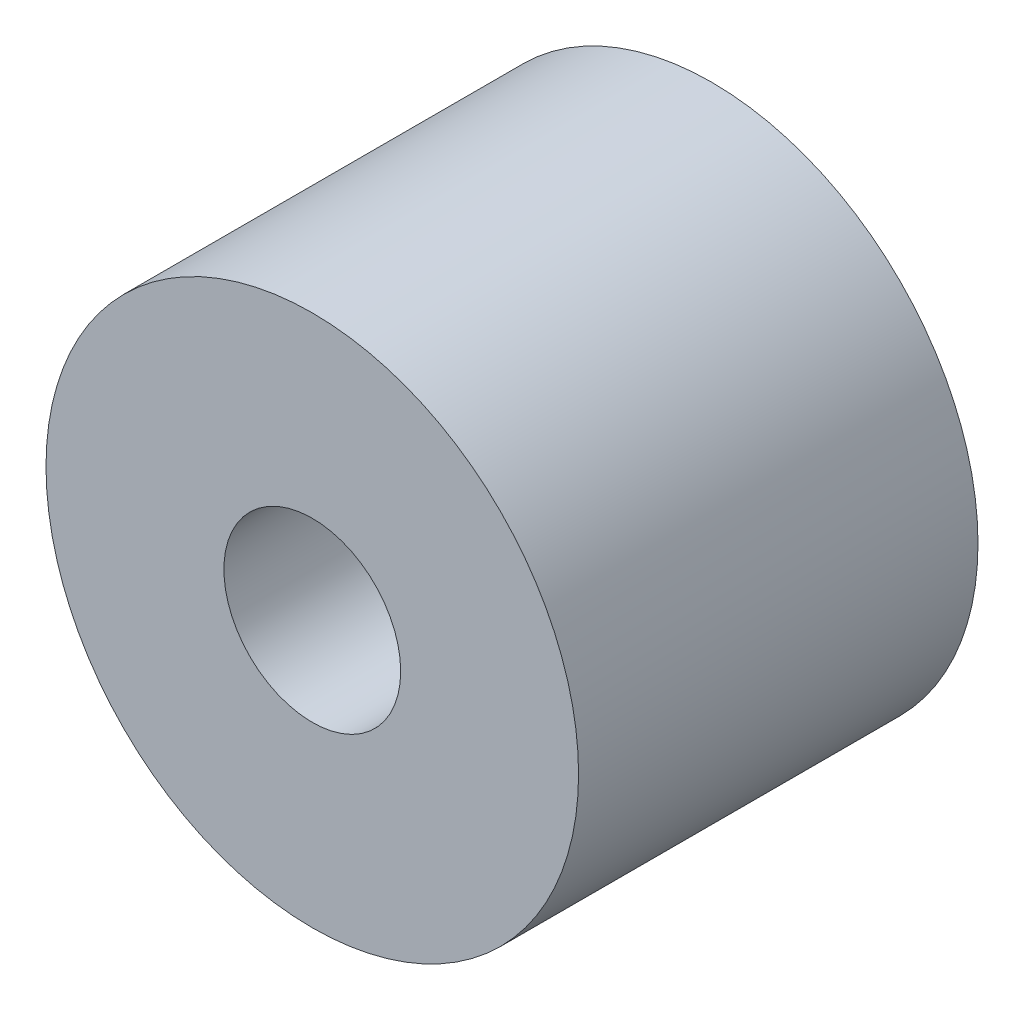
SolidWorks part; units mm, degrees
ref_plane "Front Plane" through (0, 0, 0) normal (0, 0, 1) x (1, 0, 0)
ref_plane "Top Plane" through (0, 0, 0) normal (0, 1, 0) x (1, 0, 0)
ref_plane "Right Plane" through (0, 0, 0) normal (1, 0, 0) x (0, 0, -1)
sketch "Sketch1" plane through (0, 0, 0) normal (0, 0, 1) x (1, 0, 0)
  circle A0 centre (0, 0) radius 6.35
  circle A1 centre (0, 0) radius 2.1082
  dimension "OD" = 12.7
  dimension "ID" = 4.2164
extrude "Extrude1" add sketch "Sketch1" along normal mid plane 9.525
sketch "Sketch2" plane through (0, 0, 0) normal (1, 0, 0) x (0, 0, -1)
  line L0 (-4.7625, -2.1082) -> (4.7625, -2.1082) construction
  line L3 (4.7625, 2.1082) -> (-4.7625, 2.1082) construction
  line L5 (-4.7625, -2.1082) -> (4.7625, -2.1082)
  line L6 (4.7625, 2.1082) -> (-4.7625, 2.1082)
sketch "Sketch4" plane through (0, 0, 4.7625) normal (0, 0, 1) x (1, 0, 0)
  line L0 (0, 0) -> (-1.4907, 1.4907)
  line L1 (0, -3.4925) -> (0, 3.4925) construction
  circle A0 centre (0, 0) radius 2.1082 construction
  dimension "D1" = 45
